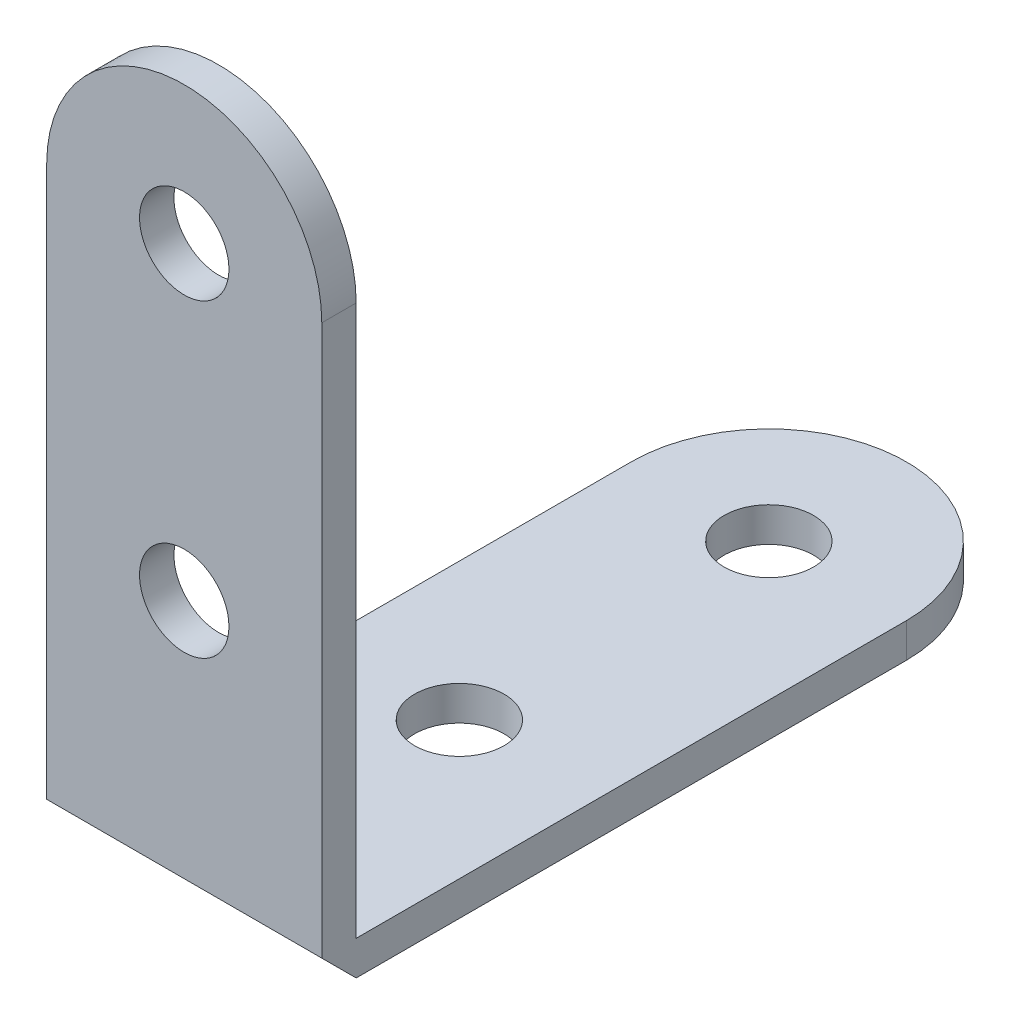
SolidWorks part; units mm, degrees
ref_plane "前视基准面" through (0, 0, 0) normal (0, 0, 1) x (1, 0, 0)
ref_plane "上视基准面" through (0, 0, 0) normal (0, 1, 0) x (1, 0, 0)
ref_plane "右视基准面" through (0, 0, 0) normal (1, 0, 0) x (0, 0, -1)
sketch "草图1" plane through (0, 0, 0) normal (0, 0, 1) x (1, 0, 0)
  line L0 (-8, 32) -> (-8, 0)
  line L1 (-8, 0) -> (8, 0)
  line L2 (8, 0) -> (8, 32)
  arc A0 (8, 32) -> (-8, 32) centre (0, 32) ccw
  circle A1 centre (0, 32) radius 2.6
  circle A2 centre (0, 14) radius 2.6
  dimension "D1" = 32
  dimension "D2" = 14
extrude "凸台-拉伸1" add sketch "草图1" along normal blind 2
sketch "草图2" plane through (0, 0, 0) normal (0, 1, 0) x (1, 0, 0)
  line L0 (-8, 32) -> (-8, 0)
  line L1 (-8, 0) -> (8, 0)
  line L2 (8, 0) -> (8, 32)
  arc A0 (8, 32) -> (-8, 32) centre (0, 32) ccw
  circle A1 centre (0, 32) radius 2.6
  circle A2 centre (0, 14) radius 2.6
extrude "凸台-拉伸2" add sketch "草图2" against normal blind 2 separate body
ref_plane "基准面1" through (8, 0, 0) normal (1, 0, 0) x (0, 0, -1)
sketch "草图3" plane through (8, 0, 0) normal (1, 0, 0) x (0, 0, -1)
  line L0 (0, 0) -> (0, -2)
  line L1 (0, -2) -> (-2, 0)
  line L2 (-2, 0) -> (0, 0)
extrude "凸台-拉伸3" add sketch "草图3" against normal up to surface (16 mm away) up to face at (-8, 16, 1)
